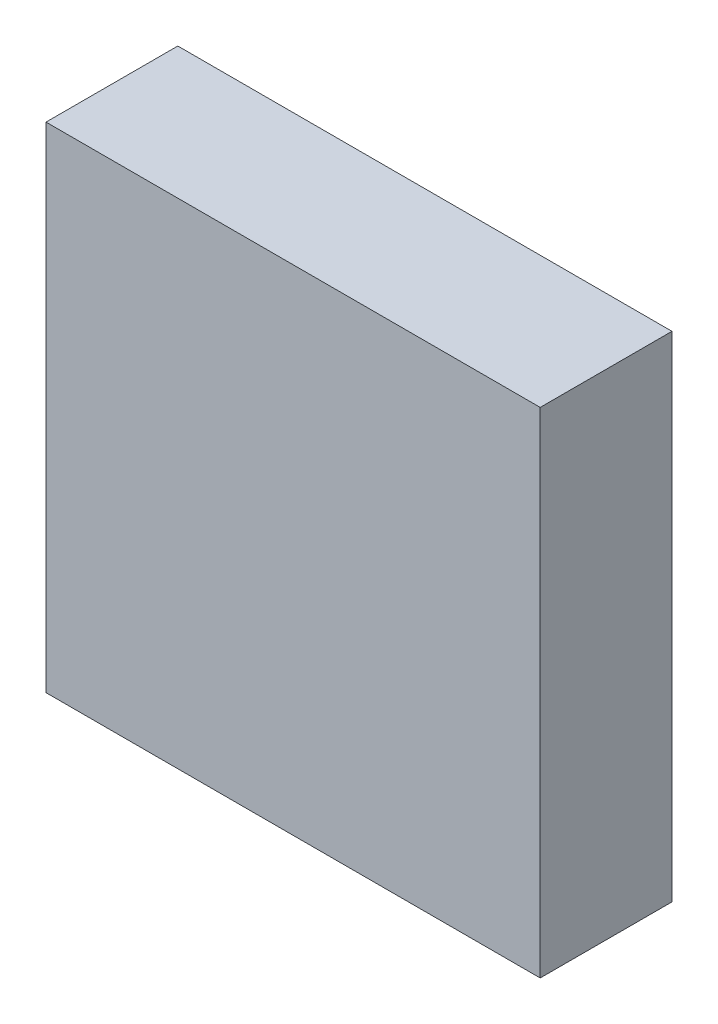
SolidWorks part; units mm, degrees
ref_plane "Plano frontal" through (0, 0, 0) normal (0, 0, 1) x (1, 0, 0)
ref_plane "Plano superior" through (0, 0, 0) normal (0, 1, 0) x (1, 0, 0)
ref_plane "Plano direito" through (0, 0, 0) normal (1, 0, 0) x (0, 0, -1)
sketch "Esboço1" plane through (0, 0, 0) normal (0, 0, 1) x (1, 0, 0)
  line L1 (0, 0) -> (150, 0)
  line L2 (0, 0) -> (0, 150)
  line L3 (0, 150) -> (150, 150)
  line L4 (150, 0) -> (150, 150)
  dimension "D1" = 150
  dimension "D2" = 150
extrude "Ressalto-extrusão1" add sketch "Esboço1" along normal blind 40
